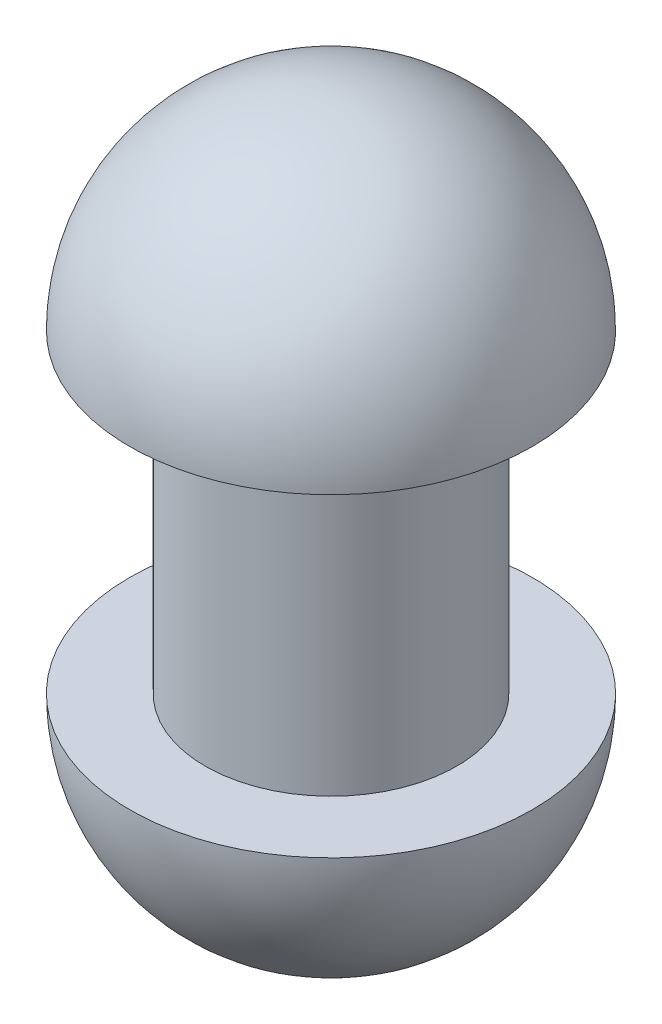
SolidWorks part; units mm, degrees
ref_plane "Front Plane" through (0, 0, 0) normal (0, 0, 1) x (1, 0, 0)
ref_plane "Top Plane" through (0, 0, 0) normal (0, 1, 0) x (1, 0, 0)
ref_plane "Right Plane" through (0, 0, 0) normal (1, 0, 0) x (0, 0, -1)
sketch "Sketch1" plane through (0, 0, 0) normal (0, 0, 1) x (1, 0, 0)
  line L4 (6.774, -3.7653) -> (6.774, 18.7347)
  line L5 (6.774, 18.7347) -> (12.174, 18.7347)
  line L8 (-2.226, 33.1347) -> (-2.226, -18.1653)
  line L10 (6.774, -3.7653) -> (12.174, -3.7653)
  arc A0 (12.174, 18.7347) -> (-2.226, 33.1347) centre (-2.226, 18.7347) ccw
  arc A1 (12.174, -3.7653) -> (-2.226, -18.1653) centre (-2.226, -3.7653) cw
revolve "Revolve1" add sketch "Sketch1" angle 360 about L8
